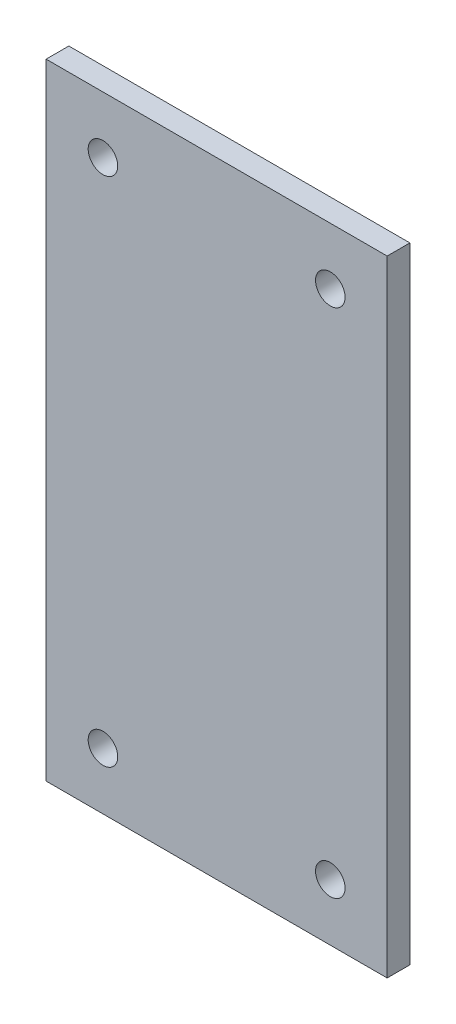
SolidWorks part; units mm, degrees
ref_plane "Спереди" through (0, 0, 0) normal (0, 0, 1) x (1, 0, 0)
ref_plane "Сверху" through (0, 0, 0) normal (0, 1, 0) x (1, 0, 0)
ref_plane "Справа" through (0, 0, 0) normal (1, 0, 0) x (0, 0, -1)
sketch "Эскиз1" plane through (0, 0, 0) normal (0, 0, 1) x (1, 0, 0)
  line L0 (150, 275) -> (-150, 275)
  line L1 (-150, 275) -> (-150, -275)
  line L2 (-150, -275) -> (150, -275)
  line L3 (150, -275) -> (150, 275)
  circle A4 centre (-100, 225) radius 13
  circle A5 centre (100, 225) radius 13
  circle A6 centre (100, -225) radius 13
  circle A7 centre (-100, -225) radius 13
extrude "Бобышка-Вытянуть1" add sketch "Эскиз1" along normal blind 20
